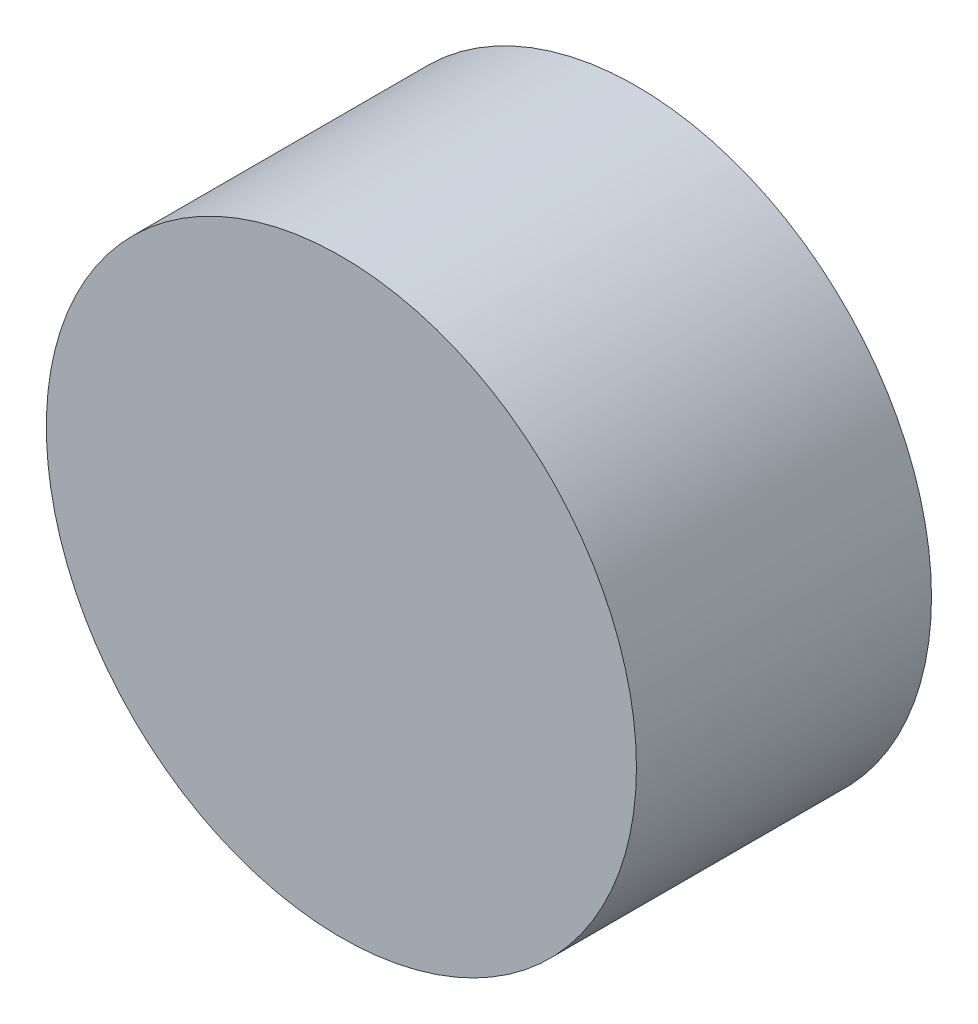
SolidWorks part; units mm, degrees
ref_plane "Front Plane" through (0, 0, 0) normal (0, 0, 1) x (1, 0, 0)
ref_plane "Top Plane" through (0, 0, 0) normal (0, 1, 0) x (1, 0, 0)
ref_plane "Right Plane" through (0, 0, 0) normal (1, 0, 0) x (0, 0, -1)
sketch "Sketch1" plane through (0, 0, 0) normal (0, 0, 1) x (1, 0, 0)
  circle A0 centre (0, 0) radius 3
  dimension "D1" = 6
extrude "Boss-Extrude1" add sketch "Sketch1" along normal blind 3
